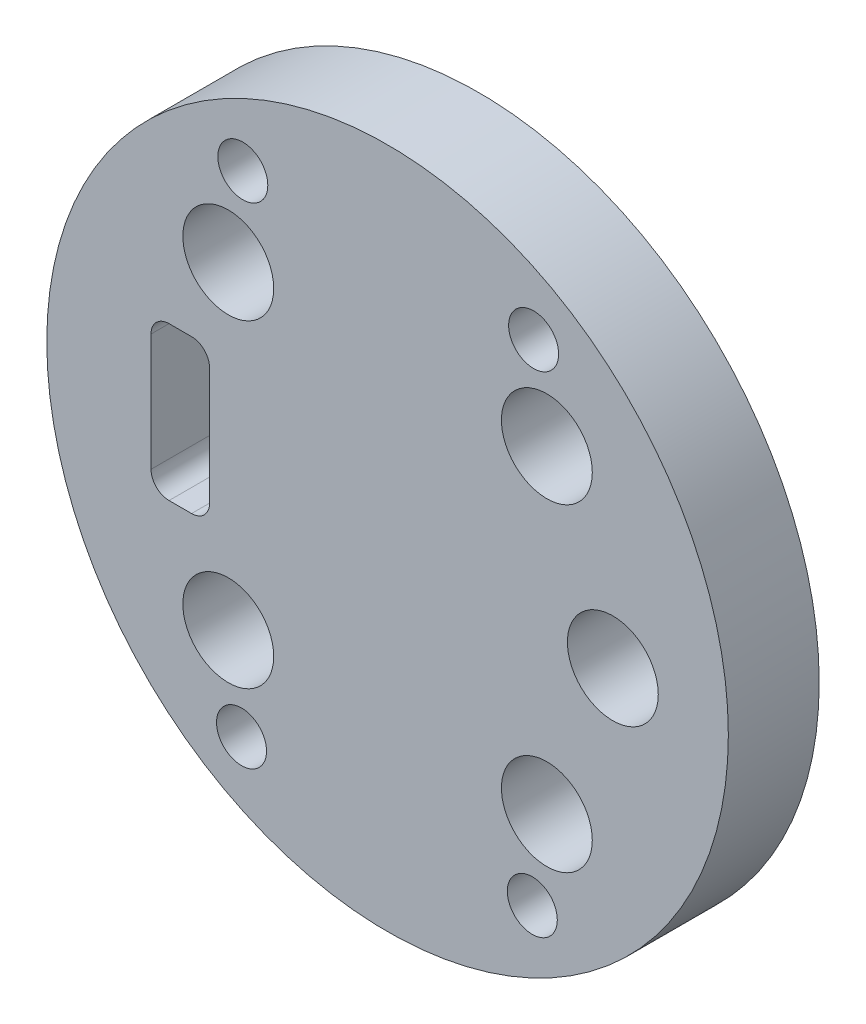
SolidWorks part; units mm, degrees
ref_plane "前视基准面" through (0, 0, 0) normal (0, 0, 1) x (1, 0, 0)
ref_plane "上视基准面" through (0, 0, 0) normal (0, 1, 0) x (1, 0, 0)
ref_plane "右视基准面" through (0, 0, 0) normal (1, 0, 0) x (0, 0, -1)
other "Configuration Table"
sketch "草图1" plane through (0, 0, 0) normal (0, 0, 1) x (1, 0, 0)
  line L0 (-21.5665, 8.4283) -> (-24.0454, 8.4283)
  line L1 (-26.0286, 6.4452) -> (-26.0286, -6.4452)
  line L2 (-24.0454, -8.4283) -> (-21.5665, -8.4283)
  line L3 (-19.5834, -6.4452) -> (-19.5834, 6.4452)
  line L4 (-19.5834, 6.4452) -> (-19.5834, -6.4452)
  arc A5 (20.7511, 17.5285) -> (14.306, 17.5285) centre (17.5285, 17.5285) ccw
  arc A6 (14.306, 17.5285) -> (20.7511, 17.5285) centre (17.5285, 17.5285) ccw
  arc A7 (27.7638, 0) -> (21.8144, 0) centre (24.7891, 0) ccw
  arc A8 (21.8144, 0) -> (27.7638, 0) centre (24.7891, 0) ccw
  arc A9 (20.7511, -17.5285) -> (14.306, -17.5285) centre (17.5285, -17.5285) ccw
  arc A10 (14.306, -17.5285) -> (20.7511, -17.5285) centre (17.5285, -17.5285) ccw
  arc A11 (-14.306, -17.5285) -> (-20.7511, -17.5285) centre (-17.5285, -17.5285) ccw
  arc A12 (-20.7511, -17.5285) -> (-14.306, -17.5285) centre (-17.5285, -17.5285) ccw
  arc A13 (-14.306, 17.5285) -> (-20.7511, 17.5285) centre (-17.5285, 17.5285) ccw
  arc A14 (-20.7511, 17.5285) -> (-14.306, 17.5285) centre (-17.5285, 17.5285) ccw
  arc A15 (-24.0454, 8.4283) -> (-26.0286, 6.4452) centre (-24.0454, 6.4452) ccw
  arc A16 (-26.0286, -6.4452) -> (-24.0454, -8.4283) centre (-24.0454, -6.4452) ccw
  arc A17 (-21.5665, -8.4283) -> (-19.5834, -6.4452) centre (-21.5665, -6.4452) ccw
  arc A18 (-19.5834, 6.4452) -> (-19.9854, 7.6422) centre (-21.5665, 6.4452) ccw
  arc A19 (-19.9854, 7.6422) -> (-21.5665, 8.4283) centre (-21.5665, 6.4452) ccw
  circle A20 centre (0, 0) radius 37.5
  dimension "D1" = 75
extrude "凸台-拉伸1" add sketch "草图1" along normal blind 10
sketch "草图2" plane through (0, 0, 10) normal (0, 0, 1) x (1, 0, 0)
  arc A0 (-20.7511, 17.5285) -> (-14.306, 17.5285) centre (-17.5285, 17.5285) ccw construction
  arc A1 (-14.306, 17.5285) -> (-20.7511, 17.5285) centre (-17.5285, 17.5285) ccw construction
  arc A2 (20.7511, 17.5285) -> (14.306, 17.5285) centre (17.5285, 17.5285) ccw construction
  arc A3 (14.306, 17.5285) -> (20.7511, 17.5285) centre (17.5285, 17.5285) ccw construction
  arc A4 (21.8144, 0) -> (27.7638, 0) centre (24.7891, 0) ccw construction
  arc A5 (27.7638, 0) -> (21.8144, 0) centre (24.7891, 0) ccw construction
  arc A6 (14.306, -17.5285) -> (20.7511, -17.5285) centre (17.5285, -17.5285) ccw construction
  arc A7 (20.7511, -17.5285) -> (14.306, -17.5285) centre (17.5285, -17.5285) ccw construction
  arc A8 (-20.7511, -17.5285) -> (-14.306, -17.5285) centre (-17.5285, -17.5285) ccw construction
  arc A9 (-14.306, -17.5285) -> (-20.7511, -17.5285) centre (-17.5285, -17.5285) ccw construction
  arc A10 (-20.7511, 17.5285) -> (-14.306, 17.5285) centre (-17.5285, 17.5285) ccw
  arc A11 (-14.306, 17.5285) -> (-20.7511, 17.5285) centre (-17.5285, 17.5285) ccw
  arc A12 (20.7511, 17.5285) -> (14.306, 17.5285) centre (17.5285, 17.5285) ccw
  arc A13 (14.306, 17.5285) -> (20.7511, 17.5285) centre (17.5285, 17.5285) ccw
  arc A14 (21.8144, 0) -> (27.7638, 0) centre (24.7891, 0) ccw
  arc A15 (27.7638, 0) -> (21.8144, 0) centre (24.7891, 0) ccw
  arc A16 (14.306, -17.5285) -> (20.7511, -17.5285) centre (17.5285, -17.5285) ccw
  arc A17 (20.7511, -17.5285) -> (14.306, -17.5285) centre (17.5285, -17.5285) ccw
  arc A18 (-20.7511, -17.5285) -> (-14.306, -17.5285) centre (-17.5285, -17.5285) ccw
  arc A19 (-14.306, -17.5285) -> (-20.7511, -17.5285) centre (-17.5285, -17.5285) ccw
  circle A20 centre (-17.5285, 17.5285) radius 5
  circle A21 centre (17.5285, 17.5285) radius 5
  circle A22 centre (-17.5285, -17.5285) radius 5
  circle A23 centre (17.5285, -17.5285) radius 5
  circle A24 centre (24.7891, 0) radius 5
  dimension "D1" = 10
  dimension "D2" = 10
  dimension "D3" = 10
  dimension "D4" = 10
  dimension "D5" = 10
extrude "切除-拉伸1" cut sketch "草图2" against normal blind 10
sketch "草图4" plane through (0, 0, 10) normal (0, 0, 1) x (1, 0, 0)
  circle A0 centre (-16.0711, -26.9578) radius 2.75
  circle A1 centre (15.9288, -27.0421) radius 2.75
  circle A2 centre (16.0711, 26.9578) radius 2.75
  circle A3 centre (-15.9288, 27.0421) radius 2.75
extrude "切除-拉伸2" cut sketch "草图4" against normal blind 10
sketch "草图5" plane through (0, 0, 0) normal (0, 0, -1) x (-1, 0, 0)
  line L0 (0, 0) -> (0, 37.5) construction
  line L1 (0, 0) -> (37.5, 0) construction
  circle A0 centre (0, 0) radius 37.5 construction
